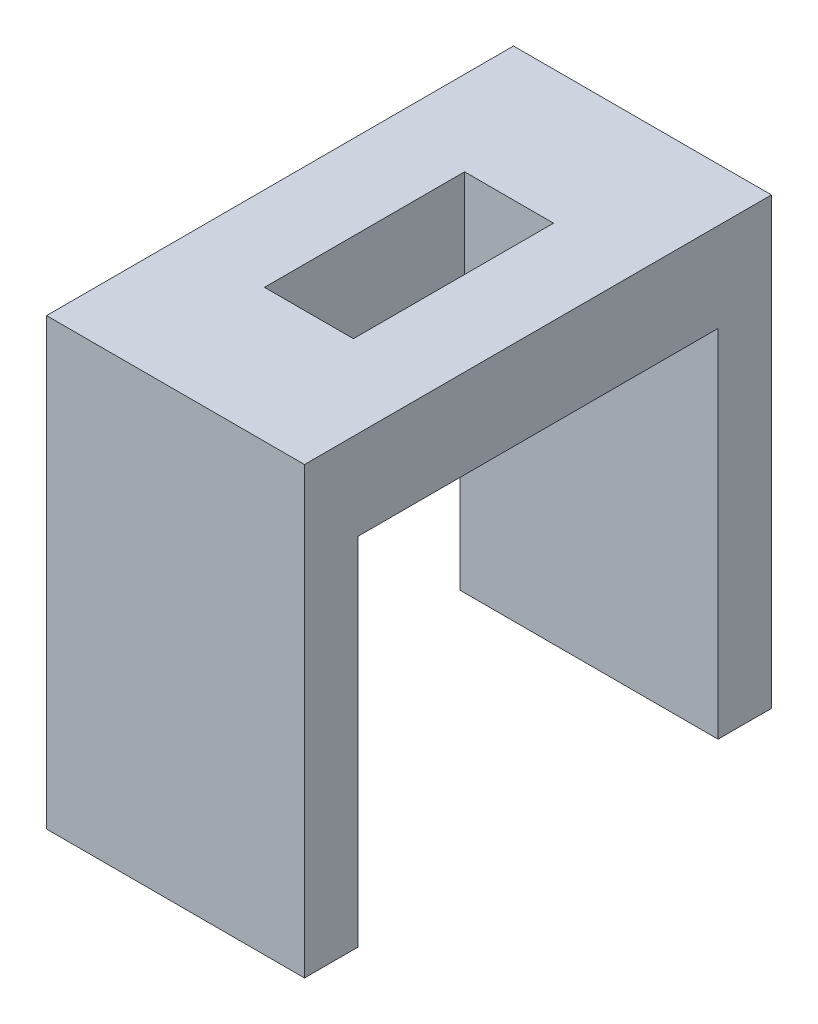
SolidWorks part; units mm, degrees
ref_plane "Alzado" through (0, 0, 0) normal (0, 0, 1) x (1, 0, 0)
ref_plane "Planta" through (0, 0, 0) normal (0, 1, 0) x (1, 0, 0)
ref_plane "Vista lateral" through (0, 0, 0) normal (1, 0, 0) x (0, 0, -1)
sketch "Croquis1" plane through (0, 0, 0) normal (0, 1, 0) x (1, 0, 0)
  line L0 (2.9, 3) -> (2.9, 0) construction
  line L1 (0, 0) -> (5.8, 0)
  line L2 (0, 0) -> (0, 10.5)
  line L3 (0, 10.5) -> (5.8, 10.5)
  line L4 (5.8, 0) -> (5.8, 10.5)
  line L5 (1.9, 7.5) -> (3.9, 7.5)
  line L6 (1.9, 7.5) -> (1.9, 3)
  line L7 (1.9, 3) -> (3.9, 3)
  line L8 (3.9, 7.5) -> (3.9, 3)
  point P9 (2.9, 3)
  point P10 (2.9, 0)
  dimension "D1" = 10.5
  dimension "D2" = 5.8
  dimension "D3" = 3
  dimension "D4" = 2
  dimension "D5" = 3
extrude "Saliente-Extruir1" add sketch "Croquis1" along normal blind 2
sketch "Croquis2" plane through (0, 0, 0) normal (0, -1, 0) x (-1, 0, 0)
  line L0 (0, 10.5) -> (0, 0) construction
  line L1 (-5.8, 10.5) -> (0, 10.5)
  line L2 (-5.8, 10.5) -> (-5.8, 9.3)
  line L3 (-5.8, 9.3) -> (0, 9.3)
  line L4 (0, 10.5) -> (0, 9.3)
  line L6 (-5.8, 0) -> (0, 0)
  line L7 (-5.8, 0) -> (-5.8, 1.2)
  line L8 (-5.8, 1.2) -> (0, 1.2)
  line L9 (0, 0) -> (0, 1.2)
  dimension "D1" = 1.2
extrude "Saliente-Extruir2" add sketch "Croquis2" along normal blind 8
